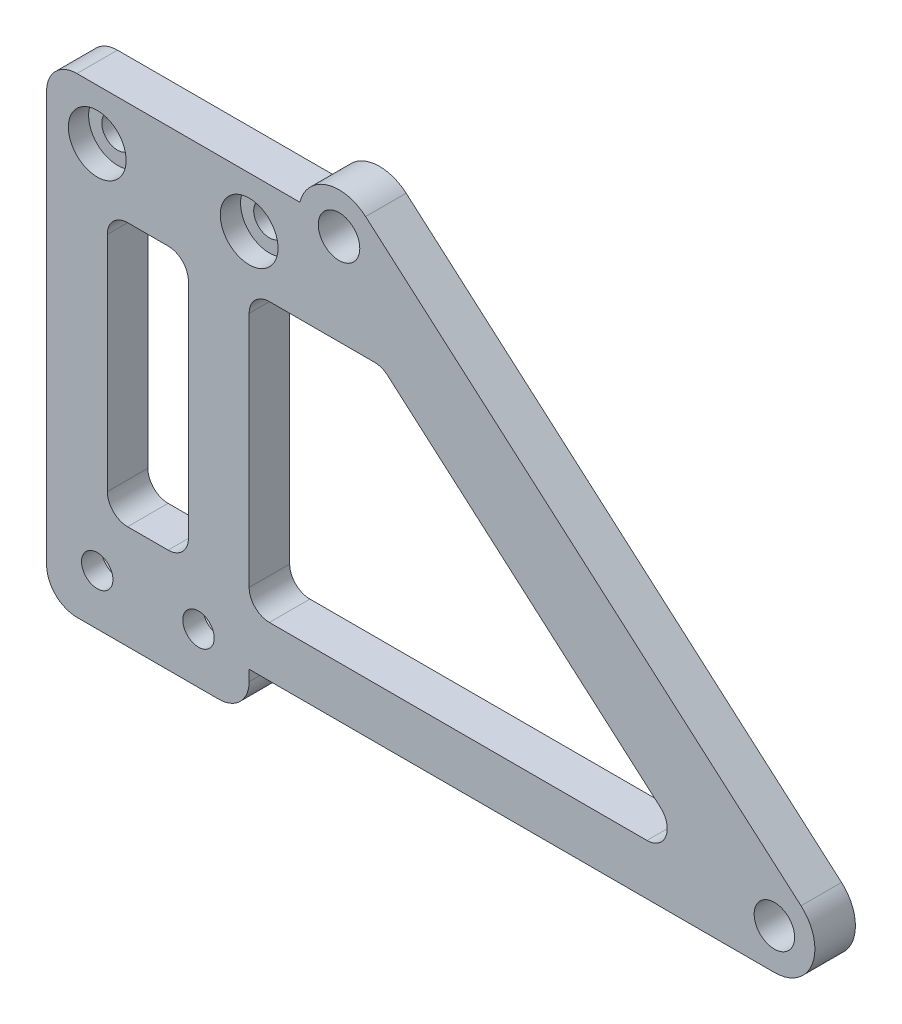
SolidWorks part; units mm, degrees
ref_plane "Front Plane" through (0, 0, 0) normal (0, 0, 1) x (1, 0, 0)
ref_plane "Top Plane" through (0, 0, 0) normal (0, 1, 0) x (1, 0, 0)
ref_plane "Right Plane" through (0, 0, 0) normal (1, 0, 0) x (0, 0, -1)
sketch "Sketch1" plane through (0, 0, 0) normal (0, 0, 1) x (1, 0, 0)
  line L0 (-25, -35.5) -> (0, -35.5) construction
  line L2 (-25, -35.5) -> (-25, -15) construction
  line L3 (-25, -35.5) -> (0, -35.5)
  line L4 (0, -35.5) -> (0, 17.15) construction
  line L5 (-25, -35.5) -> (-25, -25.5)
  line L6 (-20, -30.5) -> (-5, -30.5) construction
  line L7 (-25, -25.5) -> (0, -25.5)
  line L9 (7.873, -26.5) -> (7.873, -35.5)
  line L10 (7.873, -35.5) -> (0, -35.5)
  line L12 (3.873, -21.5) -> (3.873, -35.5) construction
  line L13 (3.873, -26.5) -> (7.873, -26.5) construction
  circle A0 centre (-20, -30.5) radius 1.55 construction
  circle A1 centre (-5, -30.5) radius 1.55 construction
  circle A2 centre (-20, -30.5) radius 1.55
  circle A3 centre (-5, -30.5) radius 1.55
  circle A4 centre (3.873, -26.5) radius 2.05
  arc A5 (7.873, -26.5) -> (0, -25.5) centre (3.873, -26.5) ccw
  dimension "D1" = 4.1
  dimension "D3" = 8
  dimension "D2" = 4
extrude "Boss-Extrude1" add sketch "Sketch1" along normal blind 4
sketch "Sketch2" plane through (0, 0, 4) normal (0, 0, 1) x (1, 0, 0)
  line L0 (7.873, -35.5) -> (7.873, -26.5) construction
  line L2 (7.873, -35.5) -> (7.873, -26.5)
  line L4 (3.873, -26.5) -> (46.8566, -63.9354) construction
  line L5 (6.5, -23.4836) -> (49.4836, -60.919)
  line L6 (44.2295, -66.9518) -> (8.1164, -35.5)
  line L7 (7.873, -35.5) -> (8.1164, -35.5)
  circle A0 centre (46.8566, -63.9354) radius 2 construction
  circle A1 centre (46.8566, -63.9354) radius 2
  arc A4 (44.2295, -66.9518) -> (49.4836, -60.919) centre (46.8566, -63.9354) ccw
  arc A5 (7.873, -26.5) -> (0, -25.5) centre (3.873, -26.5) ccw construction
  arc A7 (7.873, -26.5) -> (6.5, -23.4836) centre (3.873, -26.5) ccw
  dimension "D1" = 8
extrude "Boss-Extrude2" add sketch "Sketch2" against normal up to surface (4 mm away) up to face at (-3.45, -30.5, 0)
sketch "Sketch3" plane through (0, -35.5, 0) normal (0, -1, 0) x (1, 0, 0)
  line L0 (-25, 4) -> (8.1164, 4) construction
  line L1 (-25, 0) -> (-5, 0)
  line L2 (-25, 0) -> (-25, 4)
  line L3 (-25, 4) -> (-5, 4)
  line L4 (-5, 0) -> (-5, 4)
  dimension "D1" = 20
extrude "Boss-Extrude3" add sketch "Sketch3" along normal up to surface (36.5 mm away)
sketch "Sketch4" plane through (0, 0, 4) normal (0, 0, 1) x (1, 0, 0)
  circle A0 centre (-20, -67) radius 1.55 construction
  circle A1 centre (-10, -67) radius 1.55 construction
  circle A2 centre (-20, -67) radius 1.55
  circle A3 centre (-10, -67) radius 1.55
extrude "Cut-Extrude1" cut sketch "Sketch4" against normal through all
sketch "Sketch5" plane through (0, 0, 0) normal (0, 0, -1) x (-1, 0, 0)
  line L1 (22.85, -68.6454) -> (22.85, -65.3546)
  line L2 (22.85, -65.3546) -> (20, -63.7091)
  line L3 (20, -63.7091) -> (17.15, -65.3546)
  line L4 (17.15, -65.3546) -> (17.15, -68.6454)
  line L5 (17.15, -68.6454) -> (20, -70.2909)
  line L6 (20, -70.2909) -> (22.85, -68.6454)
  line L7 (12.85, -68.6454) -> (12.85, -65.3546)
  line L8 (12.85, -65.3546) -> (10, -63.7091)
  line L9 (10, -63.7091) -> (7.15, -65.3546)
  line L10 (7.15, -65.3546) -> (7.15, -68.6454)
  line L11 (7.15, -68.6454) -> (10, -70.2909)
  line L12 (10, -70.2909) -> (12.85, -68.6454)
  circle A0 centre (20, -67) radius 2.85 construction
  circle A1 centre (10, -67) radius 2.85 construction
  dimension "D1" = 5.7
extrude "Cut-Extrude2" cut sketch "Sketch5" against normal blind 2
sketch "Sketch6" plane through (0, 0, 0) normal (0, 0, -1) x (-1, 0, 0)
  line L0 (-46.8566, -67.9354) -> (5, -67.9354)
  line L1 (5, -72) -> (5, -35.5) construction
  line L2 (5, -67.9354) -> (5, -62.9354)
  line L3 (5, -62.9354) -> (-39.6179, -62.9354)
  line L4 (-44.2295, -66.9518) -> (-8.1164, -35.5) construction
  line L12 (25, -72) -> (25, -25.5)
  line L13 (25, -25.5) -> (0, -25.5)
  line L14 (-6.5, -23.4836) -> (-49.4836, -60.919)
  line L15 (-44.2295, -66.9518) -> (-8.1164, -35.5)
  line L16 (-8.1164, -35.5) -> (5, -35.5)
  line L17 (5, -35.5) -> (5, -72)
  line L18 (5, -72) -> (25, -72)
  line L22 (-44.2295, -66.9518) -> (-39.6179, -62.9354)
  line L24 (5, -62.9354) -> (5, -67.9354)
  arc A0 (-49.4836, -60.919) -> (-44.2295, -66.9518) centre (-46.8566, -63.9354) ccw construction
  arc A3 (0, -25.5) -> (-6.5, -23.4836) centre (-3.873, -26.5) ccw
  arc A4 (-49.4836, -60.919) -> (-44.2295, -66.9518) centre (-46.8566, -63.9354) ccw
  arc A6 (-46.8566, -67.9354) -> (-44.2295, -66.9518) centre (-46.8566, -63.9354) ccw
  arc M27 (-49.4836, -60.919) -> (-44.2295, -66.9518) centre (-46.8566, -63.9354) ccw
  line M28 (-44.2295, -66.9518) -> (-8.1164, -35.5)
  line M30 (5, -35.5) -> (5, -72)
  dimension "D1" = 5
  dimension "D2" = 0
extrude "Boss-Extrude4" add sketch "Sketch6" against normal up to surface (4 mm away) contours L3 L0 M30 M28 M27 up to face at (-8.45, -67, 4)
fillet "Fillet1" radius 2 4 edges at (39.6179, -62.9354, 2) (8.1164, -35.5, 2) (-5, -35.5, 2) (-5, -62.9354, 2)
fillet "Fillet2" radius 3 3 edges at (-5, -72, 2) (-25, -72, 2) (-25, -25.5, 2)
sketch "Sketch7" plane through (0, 0, 0) normal (0, 0, -1) x (-1, 0, 0)
  line L0 (15, -72) -> (15, -25.5) construction
  line L1 (8, -72) -> (22, -72) construction
  line L2 (0, -25.5) -> (22, -25.5) construction
  line L3 (25, -48.75) -> (5, -48.75) construction
  line L4 (11, -35.75) -> (19, -35.75)
  line L5 (11, -35.75) -> (11, -61.75)
  line L6 (11, -61.75) -> (19, -61.75)
  line L7 (19, -35.75) -> (19, -61.75)
  line L8 (25, -28.5) -> (25, -69) construction
  line L9 (5, -60.9354) -> (5, -37.5) construction
  dimension "D1" = 6
  dimension "D2" = 26
extrude "Cut-Extrude3" cut sketch "Sketch7" against normal blind 10
fillet "Fillet3" radius 2 4 edges at (-11, -35.75, 2) (-19, -35.75, 2) (-19, -61.75, 2) (-11, -61.75, 2)
sketch "Sketch8" plane through (0, 0, 4) normal (0, 0, 1) x (1, 0, 0)
  circle A0 centre (-20, -30.5) radius 2.85
  circle A1 centre (-5, -30.5) radius 2.85
  dimension "D1" = 5.7
extrude "Cut-Extrude4" cut sketch "Sketch8" against normal offset from surface (2 mm away) 2 up to face at (-15, -48.75, 0)
